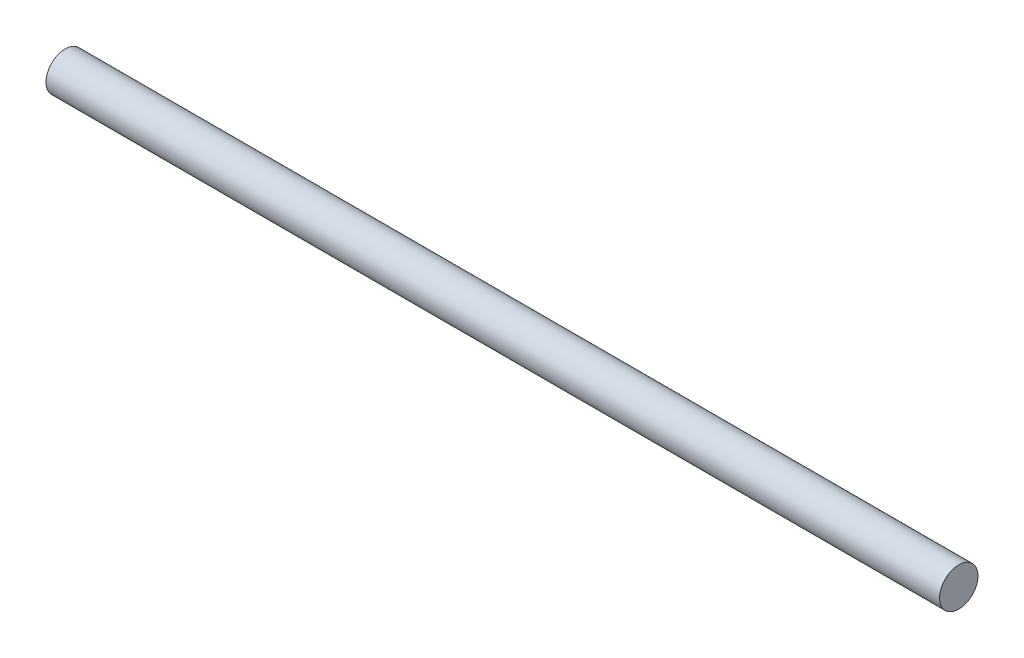
SolidWorks part; units mm, degrees
material "Cast Alloy Steel"
ref_plane "Front Plane" through (0, 0, 0) normal (0, 0, 1) x (1, 0, 0)
ref_plane "Top Plane" through (0, 0, 0) normal (0, 1, 0) x (1, 0, 0)
ref_plane "Right Plane" through (0, 0, 0) normal (1, 0, 0) x (0, 0, -1)
sketch "Sketch1" plane through (0, 0, 0) normal (1, 0, 0) x (0, 0, -1)
  circle A0 centre (0, 0) radius 6.35
  dimension "D1" = 12.7
extrude "Boss-Extrude1" add sketch "Sketch1" along normal blind 295.275
ref_plane "Plane1" through (147.6375, 0, 0) normal (1, 0, 0) x (0, 0, -1)
